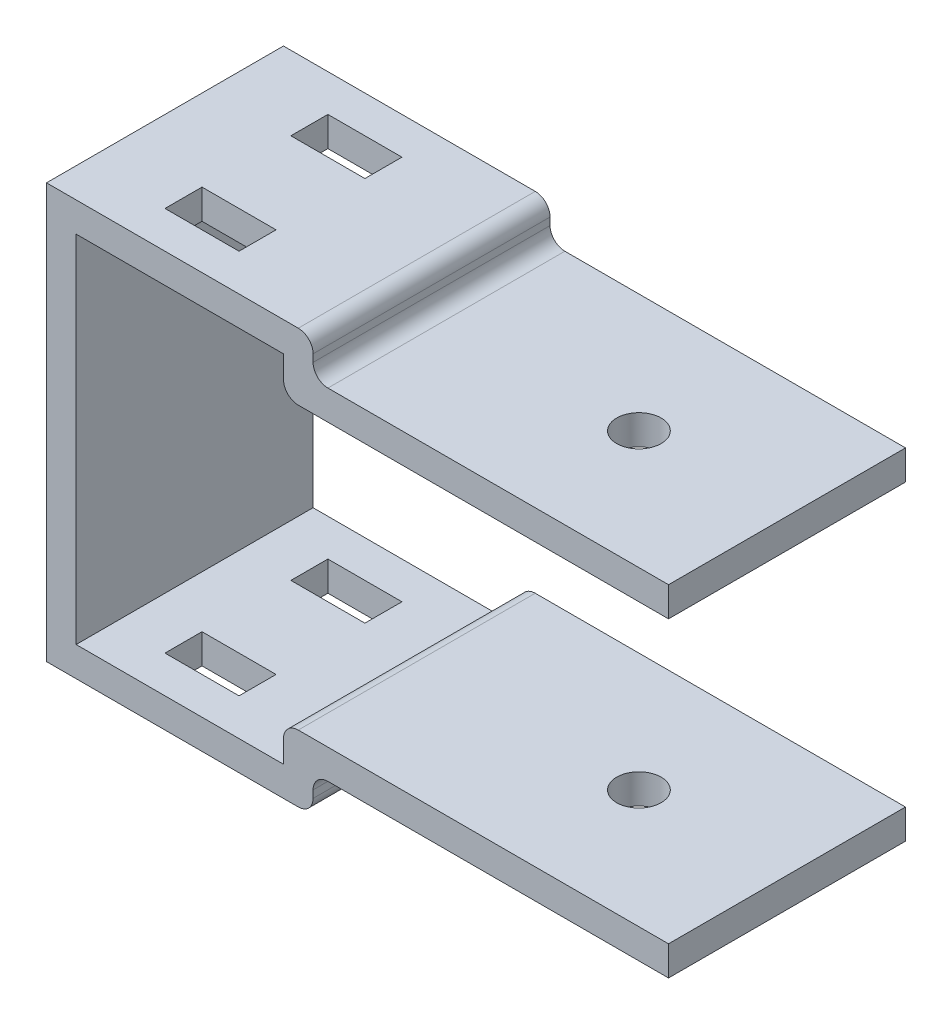
SolidWorks part; units mm, degrees
ref_plane "Ön Düzlem" through (0, 0, 0) normal (0, 0, 1) x (1, 0, 0)
ref_plane "Üst Düzlem" through (0, 0, 0) normal (0, 1, 0) x (1, 0, 0)
ref_plane "Sağ Düzlem" through (0, 0, 0) normal (1, 0, 0) x (0, 0, -1)
sketch "Çizim1" plane through (0, 0, 0) normal (0, 0, 1) x (1, 0, 0)
  line L0 (-27.0006, 0) -> (23.0087, 0) construction
  line L5 (-12.9994, 12) -> (-27.0006, 12)
  line L6 (-27.0006, 12) -> (-27.0006, -12)
  line L7 (-27.0006, -12) -> (-13.0006, -12)
  line L8 (-12.9994, 14) -> (-29.0006, 14)
  line L9 (-29.0006, 14) -> (-29.0006, -14)
  line L10 (-29.0006, -14) -> (-12.8676, -14)
  line L13 (-27.0006, 0) -> (-13.0006, 0)
  line L15 (-11.9994, 9.5) -> (13.0006, 9.5)
  line L17 (-12.0006, -9.5) -> (12.9994, -9.5)
  line L19 (-12.9994, 9.5) -> (12.9994, -9.5) construction
  line L20 (-13.0006, -9.5) -> (13.0006, 9.5) construction
  line L21 (-10.0006, -11.5) -> (12.9994, -11.5)
  line L23 (-9.9994, 11.5) -> (13.0006, 11.5)
  line L26 (-13.0006, -10.5) -> (-13.0006, -12)
  line L27 (23.0087, 14) -> (-29.0006, 14) construction
  line L28 (23.0087, 12) -> (-27.0006, 12) construction
  line L29 (-29.0006, -14) -> (23.0087, -14) construction
  line L30 (-27.0006, -12) -> (23.0087, -12) construction
  line L31 (-14.9992, 11.5) -> (-15.0008, -11.5) construction
  line L32 (-12.9994, 9.5) -> (-13.0006, -9.5) construction
  line L33 (-14.9992, 11.5) -> (15.0008, 11.5) construction
  line L34 (-15.0008, -11.5) -> (14.9992, -11.5) construction
  line L35 (13.0006, 9.5) -> (12.9994, -9.5) construction
  line L36 (15.0008, 11.5) -> (14.9992, -11.5) construction
  line L37 (13.0006, 9.5) -> (13.0006, 11.5)
  line L38 (12.9994, -9.5) -> (12.9994, -11.5)
  line L39 (-12.9994, 14) -> (-11.9994, 14)
  line L40 (-10.9994, 13) -> (-10.9994, 12.5)
  line L41 (-12.8676, -14) -> (-12.0006, -14)
  line L42 (-11.0006, -13) -> (-11.0006, -12.5)
  line L43 (-12.9994, 12) -> (-12.9994, 10.5)
  line L44 (-13.0006, -9.5) -> (12.9994, -9.5) construction
  line L45 (-12.9994, 9.5) -> (13.0006, 9.5) construction
  arc A0 (-12.0006, -14) -> (-11.0006, -13) centre (-12.0006, -13) ccw
  arc A1 (-10.0006, -11.5) -> (-11.0006, -12.5) centre (-10.0006, -12.5) ccw
  arc A2 (-13.0006, -10.5) -> (-12.0006, -9.5) centre (-12.0006, -10.5) cw
  arc A3 (-10.9994, 12.5) -> (-9.9994, 11.5) centre (-9.9994, 12.5) ccw
  arc A4 (-11.9994, 9.5) -> (-12.9994, 10.5) centre (-11.9994, 10.5) cw
  arc A5 (-11.9994, 14) -> (-10.9994, 13) centre (-11.9994, 13) cw
  point P11 (0, 0)
  dimension "D7" = 1
  dimension "D1" = 12
  dimension "D2" = 12
  dimension "D3" = 2
  dimension "D4" = 14
  dimension "D5" = 19
  dimension "D8" = 2
  dimension "D9" = 2
  dimension "D10" = 25
  dimension "D11" = 25
  dimension "D12" = 14.0013
  dimension "D13" = 14
  dimension "D14" = 24
  dimension "D15" = 2
  dimension "D6" = 2
extrude "Yükseklik-Ekstrüzyon1" add sketch "Çizim1" along normal mid plane 16 contours A5 L39 L8 L9 L10 L41 A0 L42 A1 L21 L38 L17 A2 L26 L7 L6 L5 L43 A4 L15 L37 L23 A3 L40
sketch "Çizim2" plane through (0, 0, 0) normal (0, 1, 0) x (1, 0, 0)
  line L1 (13.0006, -8) -> (13.0006, 8) construction
  line L2 (-9.9994, 8) -> (13.0006, 8) construction
  circle A0 centre (3.0006, 0) radius 1.5
  dimension "D1" = 3
  dimension "D2" = 10
  dimension "D3" = 8
extrude "Kes-Ekstrüzyon1" cut sketch "Çizim2" against normal mid plane 36
sketch "Çizim3" plane through (0, 14, 0) normal (0, 1, 0) x (1, 0, 0)
  line L0 (-29.0006, 8) -> (-11.9994, 8) construction
  line L1 (-23.5006, -3) -> (-18.5006, -3)
  line L2 (-23.5006, -3) -> (-23.5006, -5.5)
  line L3 (-23.5006, -5.5) -> (-18.5006, -5.5)
  line L4 (-18.5006, -3) -> (-18.5006, -5.5)
  line L5 (-23.5006, -3) -> (-18.5006, -5.5) construction
  line L6 (-23.5006, -5.5) -> (-18.5006, -3) construction
  line L7 (-23.5006, 5.5) -> (-18.5006, 5.5)
  line L8 (-23.5006, 5.5) -> (-23.5006, 3)
  line L9 (-23.5006, 3) -> (-18.5006, 3)
  line L10 (-18.5006, 5.5) -> (-18.5006, 3)
  line L11 (-23.5006, 5.5) -> (-18.5006, 3) construction
  line L12 (-23.5006, 3) -> (-18.5006, 5.5) construction
  line L13 (-29.0006, -8) -> (-11.9994, -8) construction
  line L14 (-29.0006, -8) -> (-29.0006, 8) construction
  point P0 (-21.0006, -4.25)
  point P5 (-21.0006, 4.25)
  dimension "D1" = 2.5
  dimension "D2" = 5
  dimension "D3" = 2.5
  dimension "D4" = 2.5
  dimension "D5" = 8
extrude "Kes-Ekstrüzyon2" cut sketch "Çizim3" against normal blind 36
